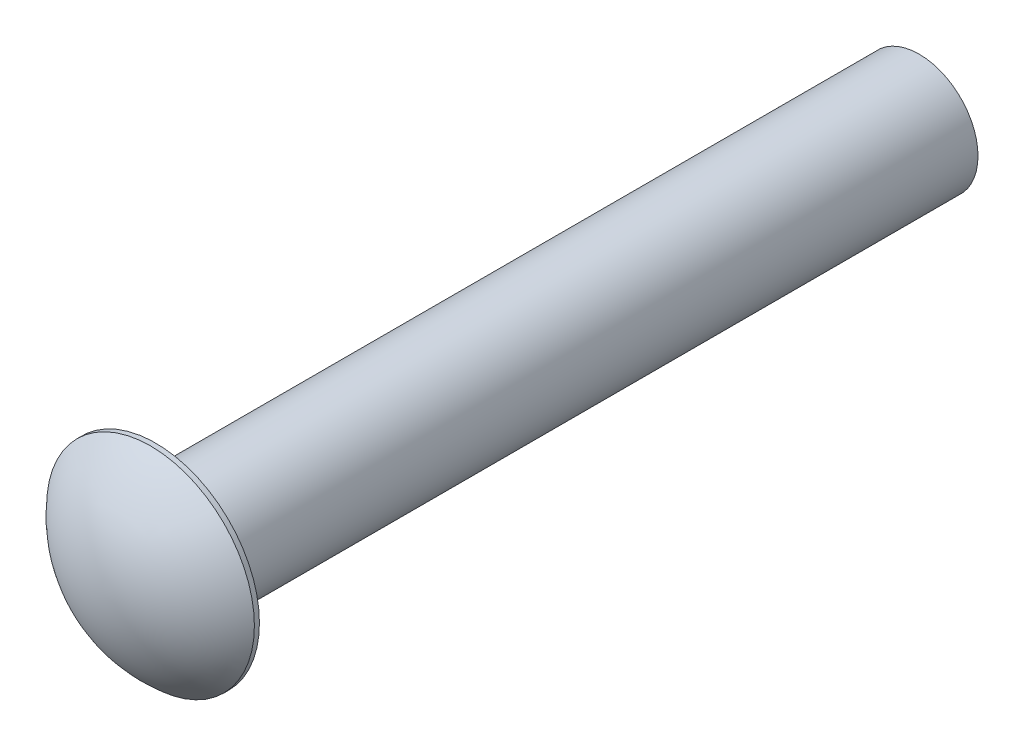
SolidWorks part; units mm, degrees
ref_plane "Front Plane" through (0, 0, 0) normal (0, 0, 1) x (1, 0, 0)
ref_plane "Top Plane" through (0, 0, 0) normal (0, 1, 0) x (1, 0, 0)
ref_plane "Right Plane" through (0, 0, 0) normal (1, 0, 0) x (0, 0, -1)
sketch "Sketch1" plane through (0, 0, 0) normal (0, 0, 1) x (1, 0, 0)
  circle A0 centre (0, 0) radius 1.7272
  dimension "D1" = 3.4544
extrude "Boss-Extrude1" add sketch "Sketch1" along normal blind 0.889
sketch "Sketch2" plane through (0, 0, 0) normal (0, 0, -1) x (-1, 0, 0)
  circle A0 centre (0, 0) radius 0.9779
  dimension "D1" = 1.9558
extrude "Boss-Extrude2" add sketch "Sketch2" along normal blind 12.7
sketch "Sketch3" plane through (0, 0, 0) normal (1, 0, 0) x (0, 0, -1)
  line L0 (0, 1.7272) -> (-0.889, 1.7272) construction
  line L2 (-0.0837, 1.7272) -> (-0.0837, 2.0447)
  line L3 (-0.0837, 2.0447) -> (-1.1527, 2.0447)
  line L4 (-1.1527, 2.0447) -> (-1.1876, 0)
  line L5 (-1.1876, 0) -> (-0.889, 0)
  arc A0 (-0.0837, 1.7272) -> (-0.889, 0) centre (1.366, 0) ccw
revolve "Cut-Revolve1" cut sketch "Sketch3" angle 360 about L5
